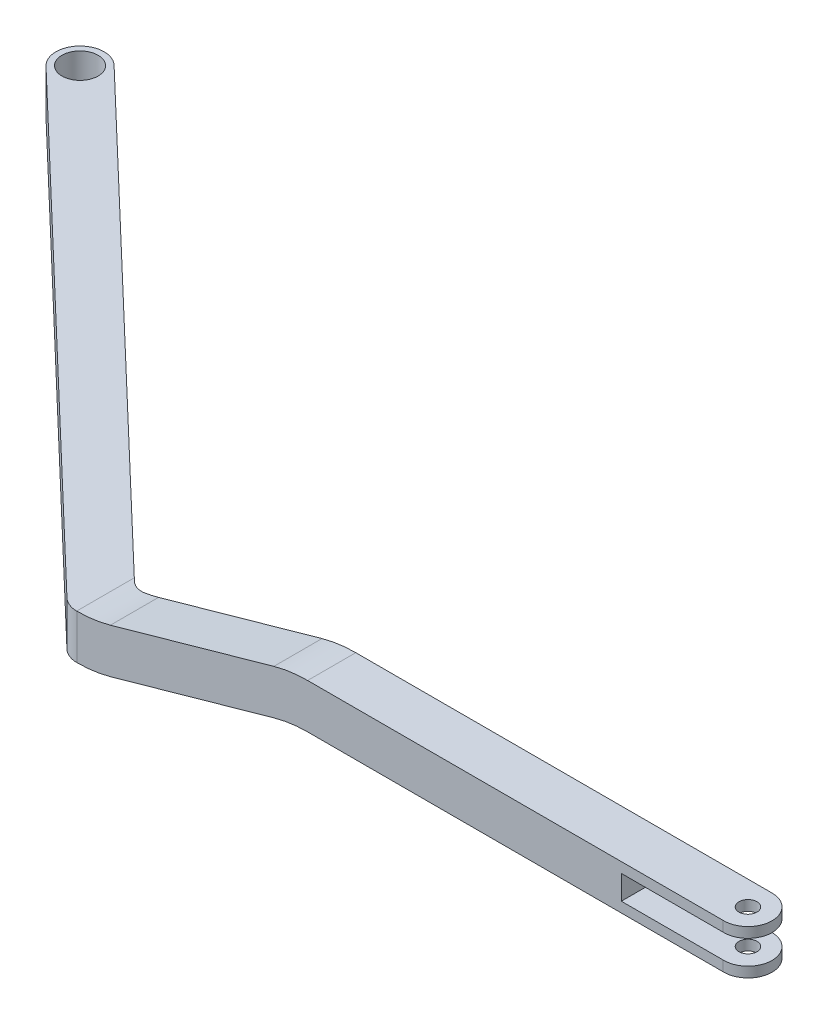
SolidWorks part; units mm, degrees
ref_plane "Front Plane" through (0, 0, 0) normal (0, 0, 1) x (1, 0, 0)
ref_plane "Top Plane" through (0, 0, 0) normal (0, 1, 0) x (1, 0, 0)
ref_plane "Right Plane" through (0, 0, 0) normal (1, 0, 0) x (0, 0, -1)
sketch "Sketch1" plane through (0, 0, 0) normal (0, 1, 0) x (1, 0, 0)
  line L0 (-1000, 0) -> (49000, 0) construction
  line L1 (0, -1000) -> (0, 49000) construction
  line L4 (36.9573, 5.2985) -> (-15.1444, 5.2985)
  line L5 (-16.7076, 1.2986) -> (36.919, 1.2986)
  line L10 (-16.7483, 1.2986) -> (-16.7076, 1.2986)
  line L11 (-16.526, 5.8525) -> (-54.4849, 42.1217)
  line L12 (-57.2482, 39.2296) -> (-18.1299, 1.8525)
  line L13 (-62.9406, 40.6756) -> (-48.7925, 40.6756) construction
  line L14 (-55.8665, 47.0703) -> (-55.8665, 34.281) construction
  line L15 (33.7123, 3.298) -> (40.2752, 3.298) construction
  line L16 (36.9937, 5.5745) -> (36.9937, 1.0214) construction
  arc A0 (36.2568, 3.4372) -> (37.7307, 3.1588) centre (36.9937, 3.298) ccw
  arc A1 (37.7307, 3.1588) -> (36.2568, 3.4372) centre (36.9937, 3.298) ccw
  arc A4 (36.919, 1.2986) -> (36.9573, 5.2985) centre (36.9937, 3.298) ccw
  arc A5 (-15.9223, 5.456) -> (-15.1444, 5.2985) centre (-15.1444, 7.2985) ccw
  arc A6 (-16.526, 5.8525) -> (-15.9223, 5.456) centre (-15.1444, 7.2985) ccw
  arc A9 (-18.1299, 1.8525) -> (-16.7483, 1.2986) centre (-16.7482, 3.2986) ccw
  circle A10 centre (-55.8665, 40.6756) radius 1.5
  arc A11 (-57.2482, 39.2296) -> (-54.4849, 42.1217) centre (-55.8665, 40.6756) cw
  point P16 (-55.8665, 40.6756)
  point P36 (-55.8665, 40.6756)
  point P37 (36.9937, 3.298)
  point P40 (36.9937, 3.298)
  dimension "D1" = 0.75
  dimension "D2" = 3
  dimension "D3" = 2.0008
  dimension "D4" = 2
  dimension "D6" = 2
  dimension "D7" = 2
  dimension "D9" = 2
  dimension "D5" = 3.9999
  dimension "D8" = 52.1017
extrude "Boss-Extrude1" add sketch "Sketch1" along normal blind 8.3
sketch "Sketch3" plane through (0, 0, -1.2986) normal (0, 0, 1) x (1, 0, 0)
  line L0 (-38.6086, 0) -> (38.6086, 0) construction
  line L1 (48.2517, 4.6) -> (48.2517, 0)
  line L2 (0, 22.829) -> (0, -22.829) construction
  line L3 (36.919, 8.3) -> (36.919, 0) construction
  line L4 (36.919, 4.6) -> (2.4378, 4.6)
  line L5 (-0.3673, 4.2126) -> (-13.9432, 0.3874)
  line L8 (36.919, 4.6) -> (38.9946, 4.6)
  line L9 (38.9946, 0) -> (38.9946, 8.3) construction
  line L13 (38.9946, 4.6) -> (48.2517, 4.6)
  line L14 (-16.7483, 3.6942) -> (-18.1299, 3.6942)
  line L15 (2.4878, 8.2942) -> (24.3532, 8.2942)
  line L16 (-13.8932, 4.0816) -> (-0.3173, 7.9068)
  line L17 (-18.1299, 8.3) -> (-18.1299, 0) construction
  line L18 (-18.1299, 3.6942) -> (-18.1299, 8.3)
  line L19 (-57.2482, 8.3) -> (-18.1299, 8.3) construction
  line L20 (-18.1299, 8.3) -> (2.6784, 8.2942)
  line L21 (-16.7483, 0) -> (48.2517, 0)
  ellipse E0 centre (2.4378, -5.4) end of major axis (12.6146, -5.4) minor radius 10 (2.4378, 4.6) -> (-0.3673, 4.2126) ccw
  ellipse E1 centre (-16.7483, 10) end of major axis (-26.925, 10) minor radius 10 (-16.7483, 0) -> (-13.9432, 0.3874) ccw
  ellipse E2 centre (2.4878, -1.7058) end of major axis (-7.6889, -1.7058) minor radius 10 (2.4878, 8.2942) -> (-0.3173, 7.9068) ccw
  ellipse E3 centre (-16.6983, 13.6942) end of major axis (-26.875, 13.6942) minor radius 10 (-16.6983, 3.6942) -> (-13.8932, 4.0816) ccw
  point P4 (0, 0)
  point P8 (0, 0)
  dimension "D1" = 65
extrude "Cut-Extrude5" cut sketch "Sketch3" against normal through all contours L13 L1 L21 E1 L5 E0 L4 L8
sketch "Sketch5" plane through (0, 0, -5.2985) normal (0, 0, -1) x (-1, 0, 0)
  line L0 (-37.4909, 4.6) -> (-35.6868, 4.6)
  line L1 (-38.9946, 4.6) -> (-36.9573, 4.6) construction
  line L2 (-36.9573, 4.6) -> (-2.4378, 4.6) construction
  line L3 (-35.6868, 4.6) -> (-35.6868, -0.9615)
  line L4 (-35.6868, -0.9615) -> (-37.7289, -0.9615)
  line L5 (-37.7289, -0.9615) -> (-37.7289, 4.6)
  line L6 (-37.7289, 4.6) -> (-37.4909, 4.6)
extrude "Cut-Extrude6" cut sketch "Sketch5" against normal through all
sketch "Sketch6" plane through (0, 0, -1.2986) normal (0, 0, 1) x (1, 0, 0)
  line L0 (-29.2997, 0) -> (29.2997, 0) construction
  line L1 (0, 20.2609) -> (0, -20.2609) construction
  line L2 (-16.7711, 3.7) -> (-18.1299, 3.7)
  line L4 (-13.9661, 4.0874) -> (-0.3901, 7.9126)
  line L6 (-18.1299, 8.3) -> (-18.1299, 0) construction
  line L8 (-18.1299, 8.3) -> (2.415, 8.3)
  line L9 (-18.1299, 3.7) -> (-46.6686, 3.7)
  line L11 (-18.1299, 8.3) -> (-46.6686, 8.3)
  line L12 (-46.6686, 3.7) -> (-46.6686, 8.3)
  ellipse E0 centre (2.415, -1.7) end of major axis (-7.7618, -1.7) minor radius 10 (2.415, 8.3) -> (-0.3901, 7.9126) ccw
  ellipse E1 centre (-16.7711, 13.7) end of major axis (-6.5944, 13.7) minor radius 10 (-16.7711, 3.7) -> (-13.9661, 4.0874) ccw
  point P4 (0, 0)
  point P8 (0, 0)
extrude "Cut-Extrude7" cut sketch "Sketch6" against normal through all
sketch "Sketch7" plane through (0, 0, -1.2986) normal (0, 0, 1) x (1, 0, 0)
  line L0 (-32.5961, 0) -> (32.5961, 0) construction
  line L1 (0, 18.4589) -> (0, -18.4589) construction
  line L2 (28.4746, 5.45) -> (38.9946, 5.45)
  line L3 (28.4746, 7.45) -> (28.4746, 5.45)
  line L4 (38.9946, 7.45) -> (28.4746, 7.45)
  line L5 (38.9946, 4.6) -> (38.9946, 8.3) construction
  line L6 (38.9946, 8.3) -> (36.919, 8.3) construction
  line L7 (38.9946, 7.45) -> (38.9946, 5.45)
  point P4 (0, 0)
  point P8 (0, 0)
  dimension "D1" = 2
  dimension "D2" = 0.85
  dimension "D3" = 10.52
extrude "Cut-Extrude8" cut sketch "Sketch7" against normal through all
sketch "Sketch9" plane through (0, 0, -5.2985) normal (0, 0, -1) x (-1, 0, 0)
  line L0 (-38.9946, 7.45) -> (-36.9573, 7.45) construction
  line L1 (-37.9625, 7.45) -> (-36.1853, 7.45)
  line L2 (-37.9625, 7.45) -> (-37.9625, 5.45)
  line L3 (-37.9625, 5.45) -> (-36.1853, 5.45)
  line L4 (-36.1853, 7.45) -> (-36.1853, 5.45)
  line L5 (-28.4746, 5.45) -> (-36.9573, 5.45) construction
extrude "Cut-Extrude11" cut sketch "Sketch9" against normal through all
sketch "Sketch12" plane through (-7.7272, 0, 8.0871) normal (-0.6908, 0, 0.723) x (0.723, 0, 0.6908)
  line L0 (-14.3879, 3.7) -> (-53.8598, 3.7) construction
  line L1 (-70.4924, 8.3) -> (-52.3745, 8.3)
  line L2 (-70.4924, 8.3) -> (-70.4924, 3.7)
  line L3 (-70.4924, 3.7) -> (-52.3745, 3.7)
  line L4 (-52.3745, 8.3) -> (-52.3745, 3.7)
extrude "Cut-Extrude12" cut sketch "Sketch12" against normal through all
